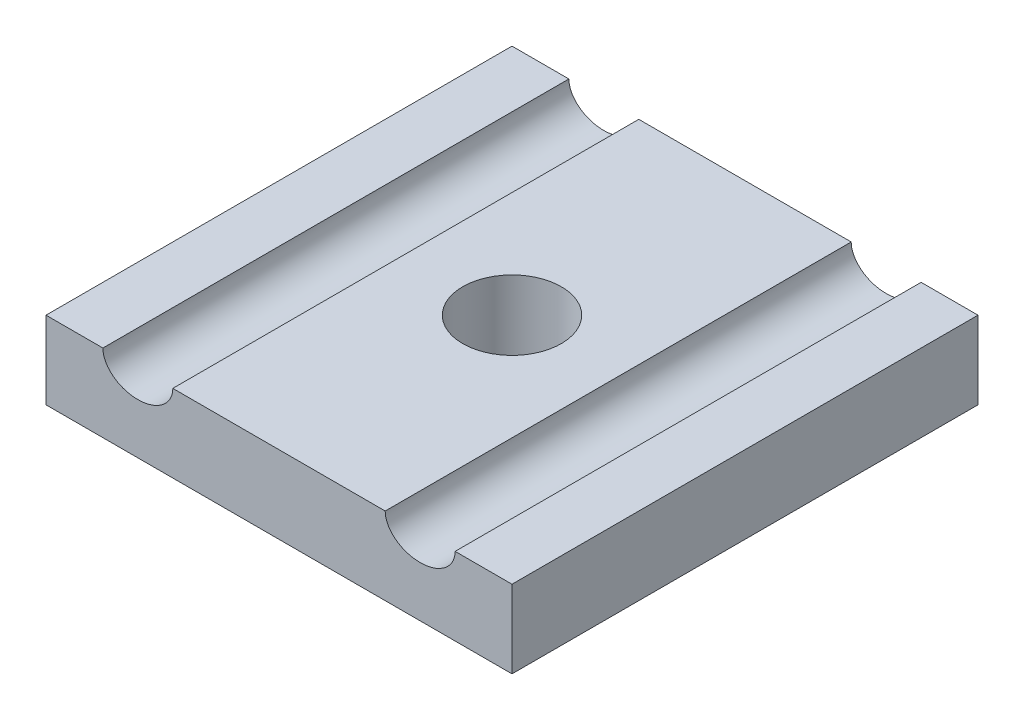
SolidWorks part; units mm, degrees
ref_plane "Front Plane" through (0, 0, 0) normal (0, 0, 1) x (1, 0, 0)
ref_plane "Top Plane" through (0, 0, 0) normal (0, 1, 0) x (1, 0, 0)
ref_plane "Right Plane" through (0, 0, 0) normal (1, 0, 0) x (0, 0, -1)
sketch "Sketch1" plane through (0, 0, 0) normal (0, 1, 0) x (1, 0, 0)
  line L1 (0, 0) -> (-30, 0)
  line L2 (0, 0) -> (0, -30)
  line L3 (0, -30) -> (-30, -30)
  line L4 (-30, 0) -> (-30, -30)
  dimension "D1" = 30
  dimension "D2" = 30
extrude "Boss-Extrude1" add sketch "Sketch1" along normal blind 5
sketch "Sketch2" plane through (0, 5, 0) normal (0, 1, 0) x (1, 0, 0)
  line L1 (0, -30) -> (0, 0) construction
  line L2 (-30, -30) -> (0, -30) construction
  circle A0 centre (-15, -15) radius 3.175
  dimension "D1" = 15
  dimension "D2" = 15
extrude "Cut-Extrude1" cut sketch "Sketch2" against normal blind 5
sketch "Sketch3" plane through (0, 0, 30) normal (0, 0, 1) x (1, 0, 0)
  line L0 (-18.175, 5) -> (-30, 5) construction
  line L1 (-11.825, 5) -> (0, 5) construction
  line L2 (-15, 5) -> (-15, 0) construction
  line L3 (-30, 5) -> (0, 5) construction
  line L4 (-30, 0) -> (0, 0) construction
  line L5 (-15, 0) -> (-11.825, 0) construction
  line L6 (-11.825, 0) -> (-11.825, 5) construction
  line L7 (-18.175, 5) -> (-18.175, 0) construction
  circle A1 centre (-5.9125, 5) radius 1.75 construction
  circle A2 centre (-24.0875, 5) radius 1.75
  ellipse E0 centre (-24.0875, 5) end of major axis (-26.3375, 5) minor radius 1.75
  ellipse E1 centre (-5.9125, 5) end of major axis (-8.1625, 5) minor radius 1.75
  dimension "D1" = 3.175
  dimension "D3" = 3.5
  dimension "D4" = 3.5
  dimension "D2" = 3.175
  dimension "D5" = 2.25
  dimension "D6" = 4.5
extrude "Cut-Extrude3" cut sketch "Sketch3" against normal up to surface (30 mm away) contours E0 | E1 up to face at (-15, 2.5, 0)
